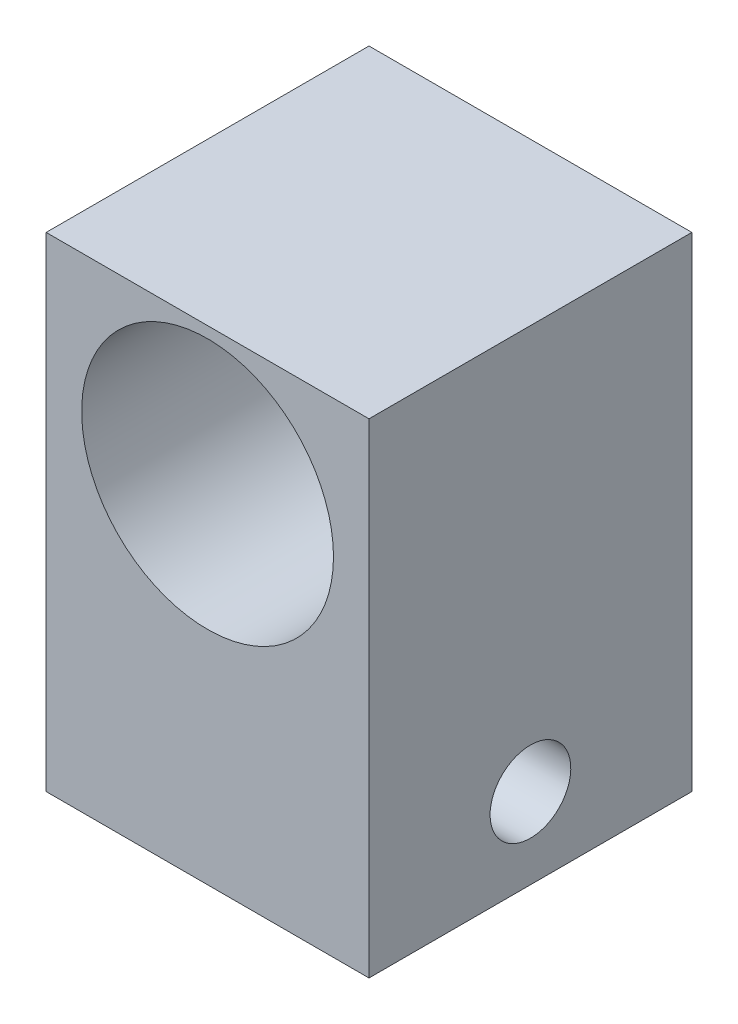
SolidWorks part; units mm, degrees
ref_plane "Front Plane" through (0, 0, 0) normal (0, 0, 1) x (1, 0, 0)
ref_plane "Top Plane" through (0, 0, 0) normal (0, 1, 0) x (1, 0, 0)
ref_plane "Right Plane" through (0, 0, 0) normal (1, 0, 0) x (0, 0, -1)
sketch "Sketch1" plane through (0, 0, 0) normal (0, 0, 1) x (1, 0, 0)
  line L1 (25.4, 38.1) -> (-25.4, 38.1)
  line L2 (25.4, 38.1) -> (25.4, -38.1)
  line L3 (25.4, -38.1) -> (-25.4, -38.1)
  line L4 (-25.4, 38.1) -> (-25.4, -38.1)
  line L5 (25.4, 38.1) -> (-25.4, -38.1) construction
  line L6 (25.4, -38.1) -> (-25.4, 38.1) construction
  point P0 (0, 0)
  dimension "D1" = 76.2
  dimension "D2" = 50.8
extrude "Boss-Extrude1" add sketch "Sketch1" along normal blind 50.8
sketch "Sketch2" plane through (0, 0, 50.8) normal (0, 0, 1) x (1, 0, 0)
  line L0 (25.4, 38.1) -> (-25.4, 38.1) construction
  circle A0 centre (0, 16.51) radius 19.812
  dimension "D1" = 39.624
  dimension "D2" = 21.59
extrude "Cut-Extrude1" cut sketch "Sketch2" against normal through all
sketch "Sketch3" plane through (25.4, 0, 0) normal (1, 0, 0) x (0, 0, -1)
  line L0 (-50.8, -38.1) -> (0, -38.1) construction
  circle A0 centre (-25.4, -25.4) radius 6.35
  point P2 (0, 0)
  point P5 (0, 0)
  point P6 (-25.4, -38.1)
  dimension "D1" = 12.7
  dimension "D2" = 12.7
extrude "Cut-Extrude2" cut sketch "Sketch3" against normal through all
